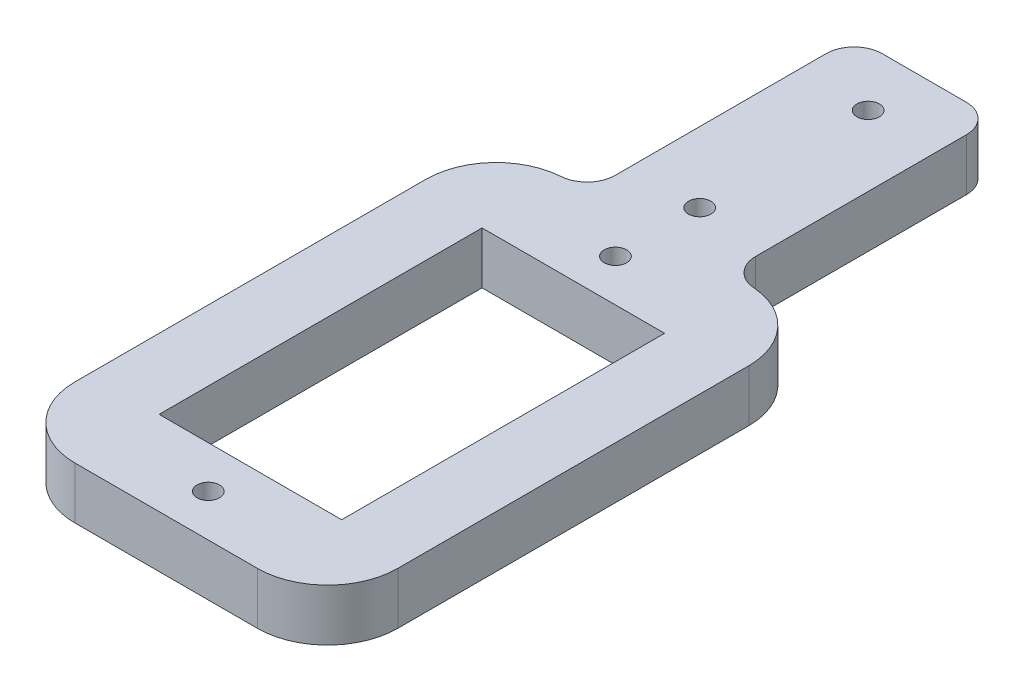
SolidWorks part; units mm, degrees
ref_plane "Front Plane" through (0, 0, 0) normal (0, 0, 1) x (1, 0, 0)
ref_plane "Top Plane" through (0, 0, 0) normal (0, 1, 0) x (1, 0, 0)
ref_plane "Right Plane" through (0, 0, 0) normal (1, 0, 0) x (0, 0, -1)
sketch "Sketch1" plane through (0, 0, 0) normal (0, 1, 0) x (1, 0, 0)
  line L1 (-6.5, 11.5) -> (6.5, 11.5)
  line L2 (-6.5, 11.5) -> (-6.5, -11.5)
  line L3 (-6.5, -11.5) -> (6.5, -11.5)
  line L4 (6.5, 11.5) -> (6.5, -11.5)
  line L5 (-6.5, 11.5) -> (6.5, -11.5) construction
  line L6 (-6.5, -11.5) -> (6.5, 11.5) construction
  line L7 (-11.5, 17.5) -> (11.5, 17.5)
  line L8 (-11.5, 17.5) -> (-11.5, -17.5)
  line L9 (-11.5, -17.5) -> (11.5, -17.5)
  line L10 (11.5, 17.5) -> (11.5, -17.5)
  line L11 (-11.5, 17.5) -> (11.5, -17.5) construction
  line L12 (-11.5, -17.5) -> (11.5, 17.5) construction
  point P0 (0, 0)
  point P6 (0, 0)
  point P11 (0, 14.5)
  point P12 (0, -14.5)
  point P13 (0, 0)
  point P22 (0, 0)
  point P23 (0, 0)
  point P40 (0, 0)
  dimension "D1" = 13
  dimension "D4" = 3
  dimension "D5" = 6.5
  dimension "D6" = 6.5
  dimension "D7" = 3
  dimension "D9" = 23
sketch "Sketch2" plane through (0, 0, 0) normal (0, 1, 0) x (1, 0, 0)
  line L0 (-6.5, 11.5) -> (-6.5, -11.5)
  line L1 (-6.5, -11.5) -> (6.5, -11.5)
  line L2 (6.5, -11.5) -> (6.5, 11.5)
  line L3 (6.5, 11.5) -> (-6.5, 11.5)
  line L4 (11.5, -17.5) -> (-11.5, -17.5)
  line L5 (-11.5, -17.5) -> (-11.5, 17.5)
  line L6 (-11.5, 17.5) -> (11.5, 17.5)
  line L7 (11.5, 17.5) -> (11.5, -17.5)
extrude "Boss-Extrude1" add sketch "Sketch2" against normal blind 3.7
sketch "Sketch3" plane through (0, 0, 0) normal (0, 1, 0) x (1, 0, 0)
  circle A0 centre (0, 14.5) radius 0.8
  circle A1 centre (0, -14.5) radius 0.8
extrude "Cut-Extrude1" cut sketch "Sketch3" against normal through all
sketch "Sketch5" plane through (0, 0, -17.5) normal (0, 0, -1) x (-1, 0, 0)
  line L0 (11.5, 0) -> (-11.5, 0) construction
  line L2 (-11.5, -3.7) -> (11.5, -3.7) construction
  line L3 (-5, 0) -> (5, 0)
  line L4 (-5, 0) -> (-5, -3.7)
  line L5 (-5, -3.7) -> (5, -3.7)
  line L6 (5, 0) -> (5, -3.7)
  line L7 (-5, 0) -> (5, -3.7) construction
  line L8 (-5, -3.7) -> (5, 0) construction
  point P0 (0, -1.85)
  point P3 (0, -1.85)
  dimension "D1" = 1.85
  dimension "D2" = 10
extrude "Boss-Extrude3" add sketch "Sketch5" along normal blind 19 contours L4 L5 L6 L3
sketch "Sketch6" plane through (0, 0, 0) normal (0, 1, 0) x (1, 0, 0)
  line L0 (0, 14.5) -> (0, 36.5)
  line L1 (5, 36.5) -> (-5, 36.5) construction
  point P5 (0, 32.5)
  point P6 (0, 20.5)
  dimension "D1" = 18
  dimension "D2" = 12
sketch "Sketch7" plane through (0, 0, 0) normal (0, 1, 0) x (1, 0, 0)
  circle A0 centre (0, 32.5) radius 0.8
  circle A1 centre (0, 20.5) radius 0.8
extrude "Cut-Extrude2" cut sketch "Sketch7" against normal through all
fillet "Fillet1" radius 5 4 edges at (11.5, -1.85, 17.5) (-11.5, -1.85, 17.5) (11.5, -1.85, -17.5) (-11.5, -1.85, -17.5)
fillet "Fillet2" radius 2 4 edges at (5, -1.85, -17.5) (-5, -1.85, -17.5) (5, -1.85, -36.5) (-5, -1.85, -36.5)
